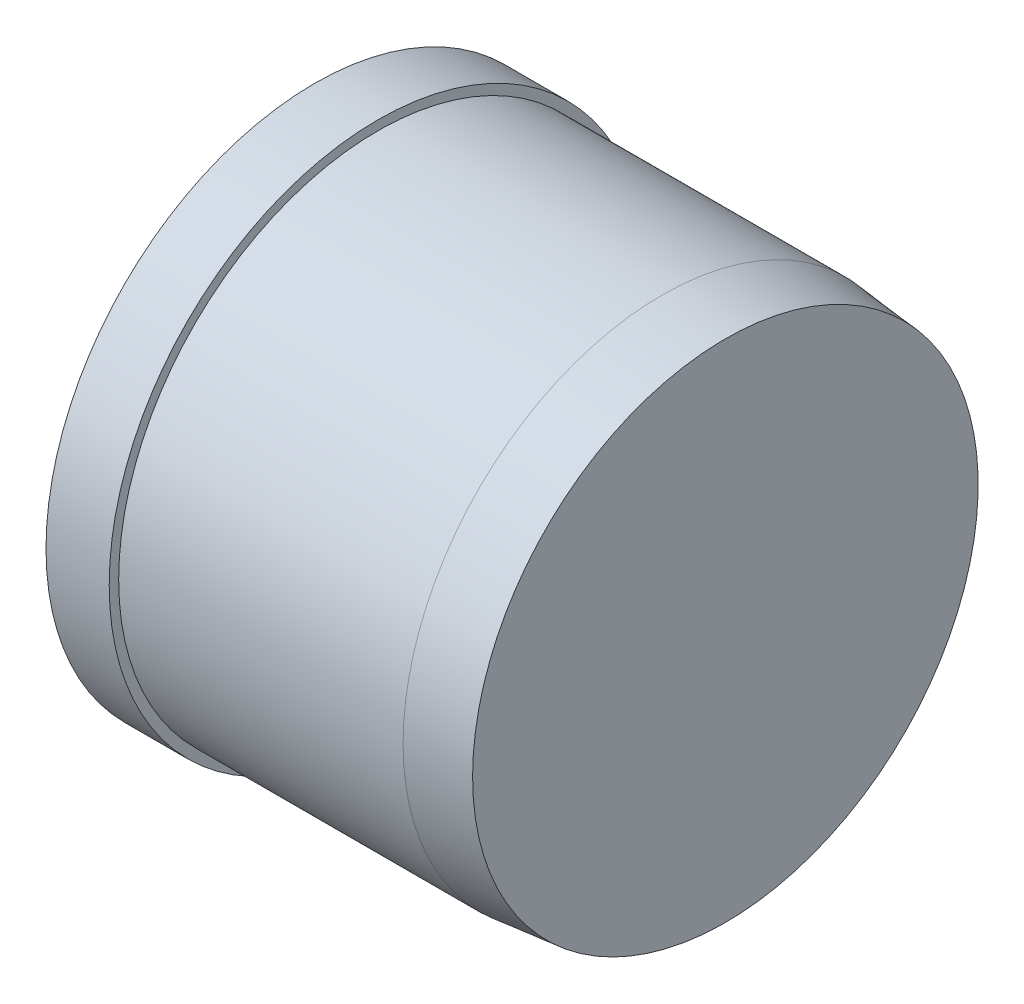
SolidWorks part; units mm, degrees
material "3003 Alloy"
ref_plane "Front Plane" through (0, 0, 0) normal (0, 0, 1) x (1, 0, 0)
ref_plane "Top Plane" through (0, 0, 0) normal (0, 1, 0) x (1, 0, 0)
ref_plane "Right Plane" through (0, 0, 0) normal (1, 0, 0) x (0, 0, -1)
sketch "Sketch1" plane through (0, 0, 0) normal (0, 0, 1) x (1, 0, 0)
  line L0 (0, 0) -> (65, 0) construction
  line L1 (65, 0) -> (65, 40)
  line L2 (65, 40) -> (55, 41)
  line L3 (55, 41) -> (10, 41)
  line L4 (10, 41) -> (10, 42.5)
  line L5 (10, 42.5) -> (0, 42.5)
  line L6 (0, 42.5) -> (0, 0)
  line L7 (0, 0) -> (65, 0)
  dimension "D1" = 42.5
  dimension "D2" = 41
  dimension "D3" = 45
  dimension "D4" = 10
  dimension "D5" = 10
  dimension "D6" = 40
revolve "Revolve1" add sketch "Sketch1" angle 360 about L0
